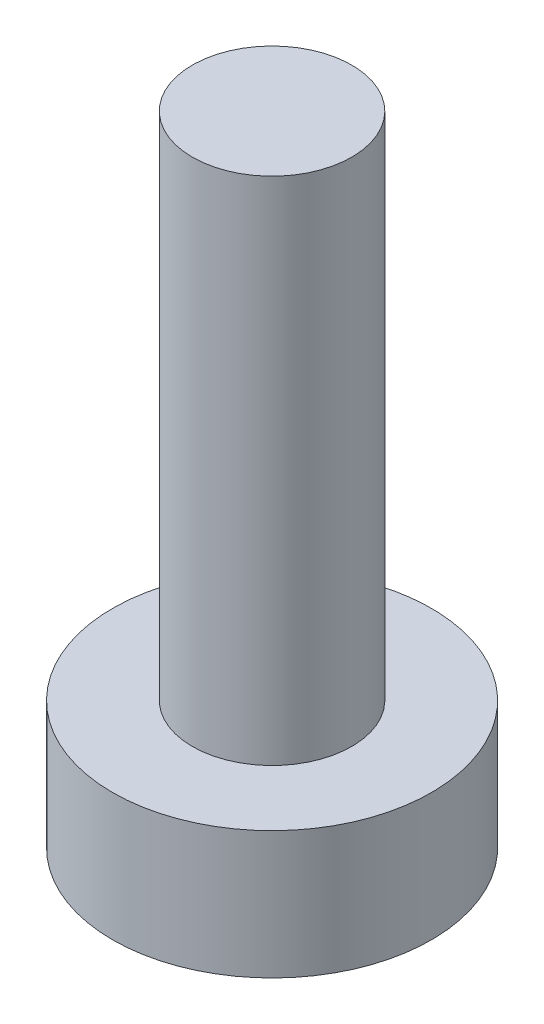
SolidWorks part; units mm, degrees
ref_plane "Front Plane" through (0, 0, 0) normal (0, 0, 1) x (1, 0, 0)
ref_plane "Top Plane" through (0, 0, 0) normal (0, 1, 0) x (1, 0, 0)
ref_plane "Right Plane" through (0, 0, 0) normal (1, 0, 0) x (0, 0, -1)
sketch "Sketch1" plane through (0, 0, 0) normal (0, 1, 0) x (1, 0, 0)
  circle A0 centre (0, 0) radius 2.5
extrude "Boss-Extrude1" add sketch "Sketch1" along normal blind 2
sketch "Sketch2" plane through (0, 2, 0) normal (0, 1, 0) x (1, 0, 0)
  circle A0 centre (0, 0) radius 1.25
extrude "Boss-Extrude2" add sketch "Sketch2" along normal blind 8
